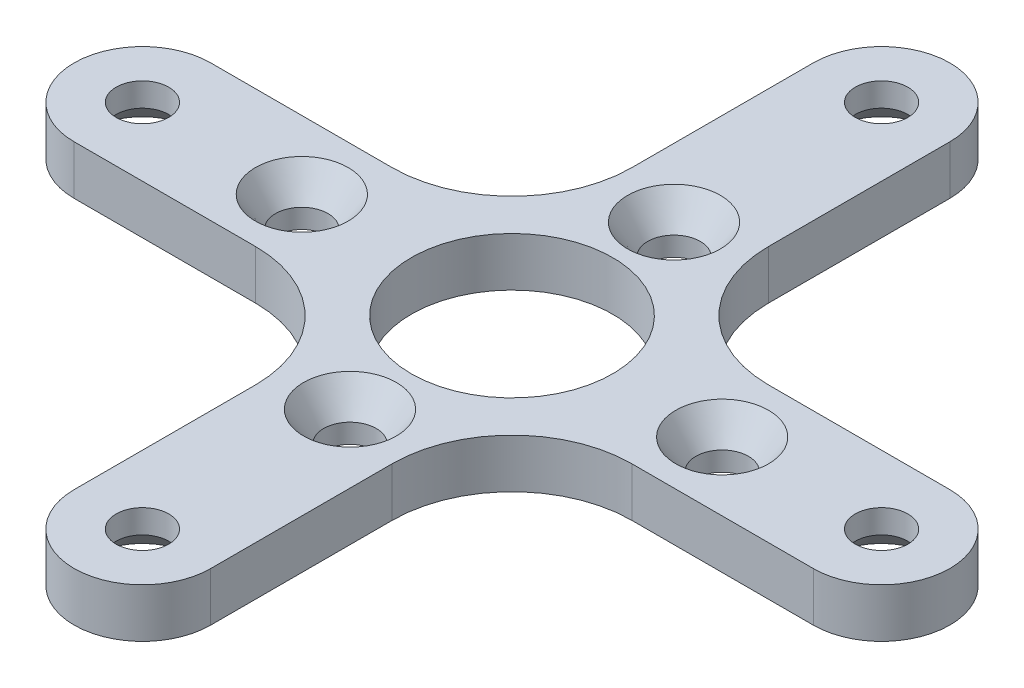
SolidWorks part; units mm, degrees
ref_plane "Front Plane" through (0, 0, 0) normal (0, 0, 1) x (1, 0, 0)
ref_plane "Top Plane" through (0, 0, 0) normal (0, 1, 0) x (1, 0, 0)
ref_plane "Right Plane" through (0, 0, 0) normal (1, 0, 0) x (0, 0, -1)
sketch "Sketch1" plane through (0, 0, 0) normal (0, 1, 0) x (1, 0, 0)
  line L0 (-12, 0) -> (12, 0) construction
  line L1 (0, -9.25) -> (0, 9.25) construction
  line L2 (-21.1, 0) -> (21.1, 0) construction
  line L3 (0, -21.1) -> (0, 21.1) construction
  line L4 (-21.1, 3.9) -> (-10.7433, 3.9)
  line L5 (-3.9, 21.1) -> (-3.9, 10.7433)
  line L6 (10.7433, 3.9) -> (21.1, 3.9)
  line L7 (3.9, 21.1) -> (3.9, 10.7433)
  line L8 (21.1, -3.9) -> (10.7433, -3.9)
  line L9 (3.9, -10.7433) -> (3.9, -21.1)
  line L10 (-3.9, -21.1) -> (-3.9, -10.7433)
  line L11 (-10.7433, -3.9) -> (-21.1, -3.9)
  line L12 (4.0659, 4.0659) -> (5.9043, 5.9043) construction
  circle A0 centre (0, 0) radius 5.75
  circle A1 centre (0, 9.25) radius 1.5
  circle A2 centre (0, 21.1) radius 1.5
  circle A3 centre (12, 0) radius 1.5
  circle A4 centre (21.1, 0) radius 1.5
  circle A5 centre (0, -9.25) radius 1.5
  circle A6 centre (0, -21.1) radius 1.5
  circle A7 centre (-12, 0) radius 1.5
  circle A8 centre (-21.1, 0) radius 1.5
  arc A9 (-3.9, 21.1) -> (3.9, 21.1) centre (0, 21.1) cw
  arc A10 (21.1, 3.9) -> (21.1, -3.9) centre (21.1, 0) cw
  arc A11 (3.9, -21.1) -> (-3.9, -21.1) centre (0, -21.1) cw
  arc A12 (-21.1, -3.9) -> (-21.1, 3.9) centre (-21.1, 0) cw
  arc A13 (-10.7433, 3.9) -> (-3.9, 10.7433) centre (-10.7433, 10.7433) ccw
  arc A14 (3.9, 10.7433) -> (10.7433, 3.9) centre (10.7433, 10.7433) ccw
  arc A15 (10.7433, -3.9) -> (3.9, -10.7433) centre (10.7433, -10.7433) ccw
  arc A16 (-3.9, -10.7433) -> (-10.7433, -3.9) centre (-10.7433, -10.7433) ccw
  point P39 (25, 0)
  point P40 (-25, 0)
  point P43 (0, 0)
  dimension "D1" = 11.5
  dimension "D2" = 3
  dimension "D3" = 7.8
  dimension "D4" = 18.5
  dimension "D5" = 24
  dimension "D6" = 50
  dimension "D7" = 2.6
extrude "Boss-Extrude1" add sketch "Sketch1" along normal mid plane 2.8
chamfer "Chamfer1" distance 1.45 angle 45 4 edges at (-21.1, -1.4, 1.5) (0, -1.4, -19.6) (21.1, -1.4, 1.5) (0, -1.4, 22.6)
chamfer "Chamfer2" distance 1.15 distance2 1.7 4 edges at (12, 1.4, 1.5) (0, 1.4, -7.75) (-12, 1.4, 1.5) (0, 1.4, 10.75)
